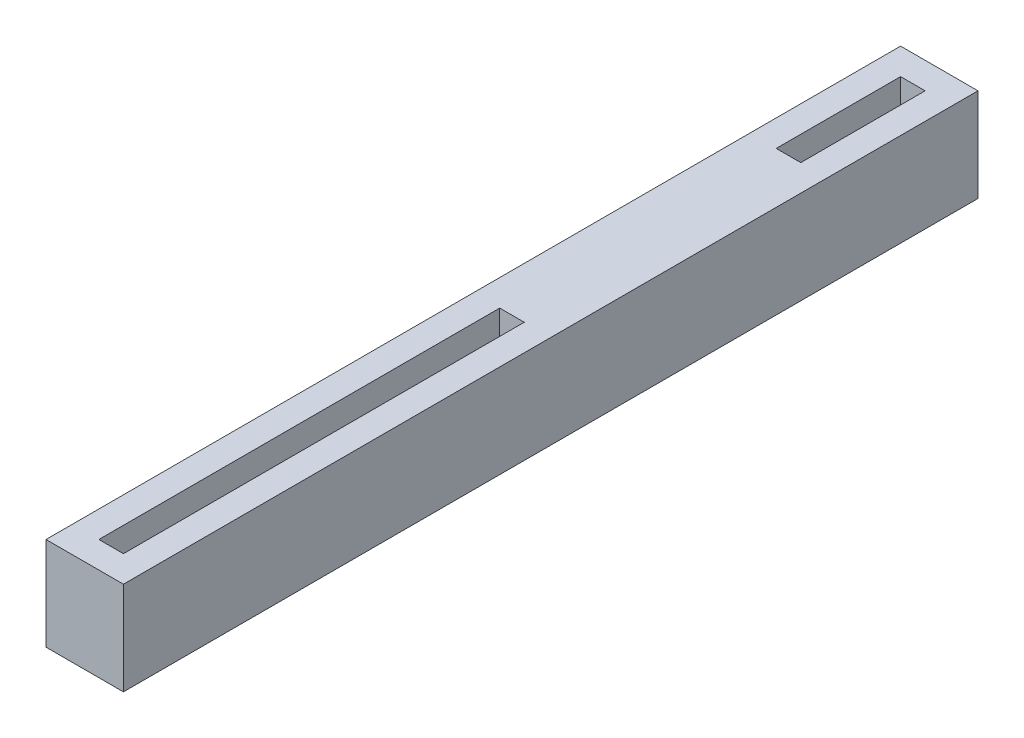
SolidWorks part; units mm, degrees
ref_plane "Front Plane" through (0, 0, 0) normal (0, 0, 1) x (1, 0, 0)
ref_plane "Top Plane" through (0, 0, 0) normal (0, 1, 0) x (1, 0, 0)
ref_plane "Right Plane" through (0, 0, 0) normal (1, 0, 0) x (0, 0, -1)
sketch "Sketch1" plane through (0, 0, 0) normal (0, 1, 0) x (1, 0, 0)
  line L0 (-14.2964, 30.5297) -> (-9.3157, 30.5297)
  line L1 (-9.3157, 30.5297) -> (-9.3157, -24.4422)
  line L2 (-9.3157, -24.4422) -> (-14.2964, -24.4422)
  line L3 (-14.2964, -24.4422) -> (-14.2964, 30.5297)
extrude "Boss-Extrude1" add sketch "Sketch1" along normal blind 6
sketch "Sketch2" plane through (0, 6, 0) normal (0, 1, 0) x (1, 0, 0)
  line L10 (-12.5964, 20.8297) -> (-11.0157, 20.8297)
  line L18 (-12.5964, 28.8297) -> (-12.5964, -22.7422)
  line L19 (-12.5964, -22.7422) -> (-11.0157, -22.7422)
  line L20 (-11.0157, -22.7422) -> (-11.0157, 28.8297)
  line L21 (-11.0157, 28.8297) -> (-12.5964, 28.8297)
  line L22 (-12.5964, 28.8297) -> (-12.5964, 20.8297)
  line L24 (-11.0157, 20.8297) -> (-11.0157, 28.8297)
  line L25 (-11.0157, 28.8297) -> (-12.5964, 28.8297)
  dimension "D2" = 8
  dimension "D1" = 1.7
extrude "Cut-Extrude2" cut sketch "Sketch2" against normal blind 7
sketch "Sketch4" plane through (0, 0, 0) normal (0, -1, 0) x (1, 0, 0)
  line L5 (-11.0157, -3.0437) -> (-12.5964, -3.0437)
  line L17 (-12.5964, 22.7422) -> (-12.5964, -28.8297)
  line L18 (-12.5964, -28.8297) -> (-11.0157, -28.8297)
  line L19 (-11.0157, -28.8297) -> (-11.0157, 22.7422)
  line L20 (-11.0157, 22.7422) -> (-12.5964, 22.7422)
  line L21 (-12.5964, 22.7422) -> (-12.5964, -3.0437)
  line L23 (-11.0157, -3.0437) -> (-11.0157, 22.7422)
  line L24 (-11.0157, 22.7422) -> (-12.5964, 22.7422)
  dimension "D2" = 1.7
extrude "Cut-Extrude3" cut sketch "Sketch4" against normal blind 7
